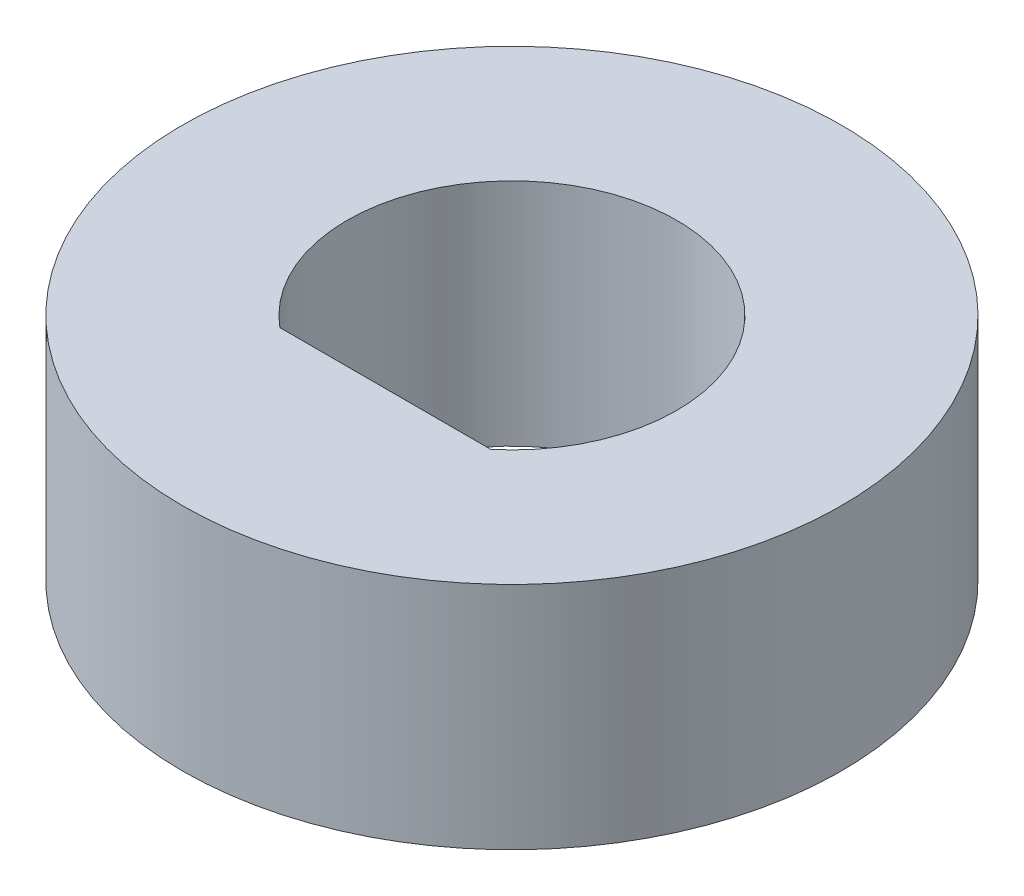
SolidWorks part; units mm, degrees
ref_plane "Front Plane" through (0, 0, 0) normal (0, 0, 1) x (1, 0, 0)
ref_plane "Top Plane" through (0, 0, 0) normal (0, 1, 0) x (1, 0, 0)
ref_plane "Right Plane" through (0, 0, 0) normal (1, 0, 0) x (0, 0, -1)
sketch "Sketch1" plane through (0, 0, 0) normal (0, 1, 0) x (1, 0, 0)
  line L0 (-2.032, -2.4396) -> (2.032, -2.4396)
  circle A0 centre (0, 0) radius 6.35
  circle A1 centre (0, 0) radius 3.175
  dimension "D1" = 6.35
  dimension "D3" = 12.7
  dimension "D2" = 4.064
extrude "Boss-Extrude1" add sketch "Sketch1" along normal blind 76.2 contours L0 A1 | A0 A1
sketch "Sketch2" plane through (0, 76.2, 0) normal (0, 1, 0) x (1, 0, 0)
  circle A0 centre (0, 0) radius 6.35
extrude "Cut-Extrude1" cut sketch "Sketch2" against normal blind 71.7728 contours A0
